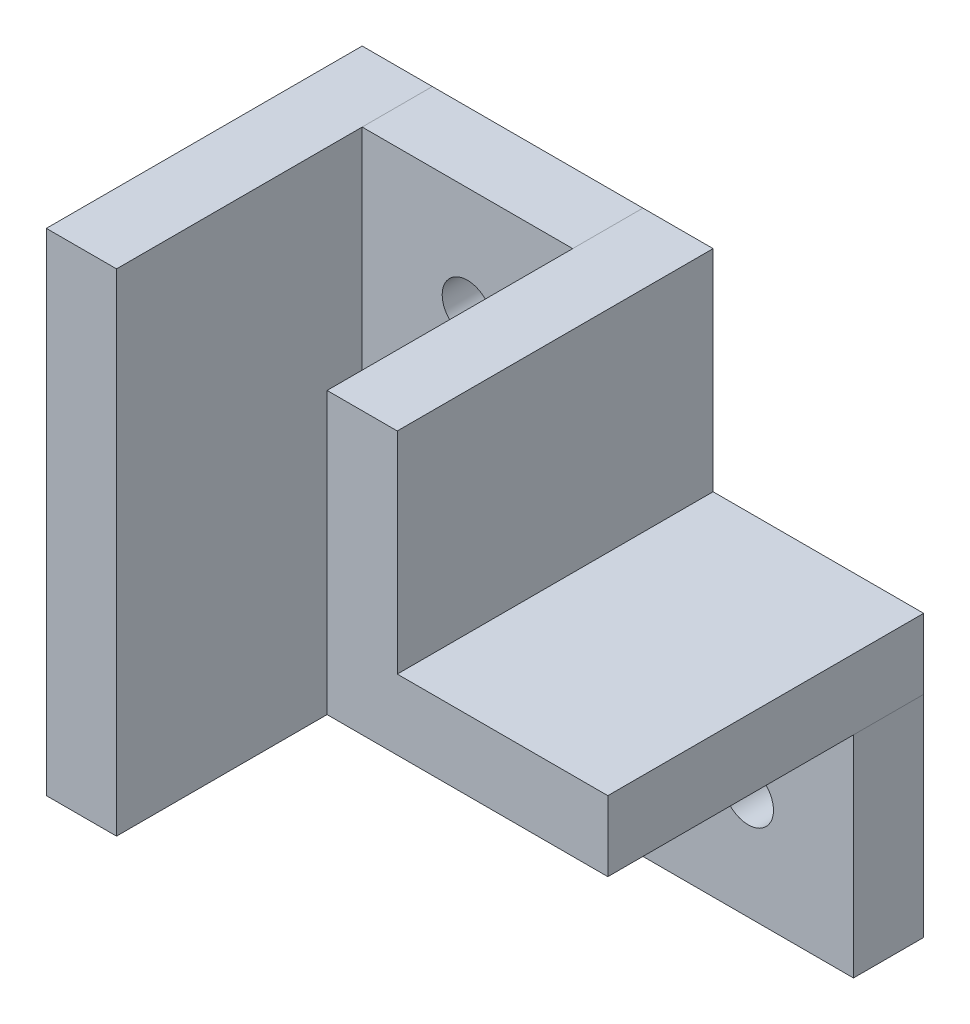
SolidWorks part; units mm, degrees
ref_plane "前视基准面" through (0, 0, 0) normal (0, 0, 1) x (1, 0, 0)
ref_plane "上视基准面" through (0, 0, 0) normal (0, 1, 0) x (1, 0, 0)
ref_plane "右视基准面" through (0, 0, 0) normal (1, 0, 0) x (0, 0, -1)
sketch "Sketch1" plane through (0, 0, 0) normal (0, 0, 1) x (1, 0, 0)
  line L0 (-7.5299, -25.8068) -> (27.4701, -25.8068)
  line L3 (-7.5299, 9.1932) -> (7.4701, 9.1932)
  line L4 (-7.5299, 9.1932) -> (-7.5299, -25.8068)
  line L6 (7.4701, 9.1932) -> (7.4701, -10.8068)
  line L7 (27.4701, -25.8068) -> (27.4701, -10.8068)
  line L8 (27.4701, -10.8068) -> (7.4701, -10.8068)
  dimension "D1" = 15
  dimension "D2" = 35
  dimension "D3" = 35
  dimension "D4" = 15
extrude "Boss-Extrude1" add sketch "Sketch1" along normal blind 5
sketch "Sketch2" plane through (0, 0, 0) normal (0, 0, -1) x (-1, 0, 0)
  line L0 (-7.4701, 9.1932) -> (-12.4701, 9.1932)
  line L1 (-12.4701, 9.1932) -> (-12.4701, -5.8068)
  line L2 (-12.4701, -5.8068) -> (-27.4701, -5.8068)
  line L3 (-27.4701, -10.8068) -> (-27.4701, -5.8068)
  line L4 (-27.4701, -10.8068) -> (-7.4701, -10.8068)
  line L5 (-7.4701, -10.8068) -> (-7.4701, 9.1932)
  dimension "D1" = 5
  dimension "D2" = 5
extrude "Boss-Extrude2" add sketch "Sketch2" against normal blind 22.5 separate body
sketch "Sketch3" plane through (0, 0, 0) normal (0, 0, -1) x (-1, 0, 0)
  line L0 (7.5299, 9.1932) -> (12.5299, 9.1932)
  line L1 (7.5299, -25.8068) -> (12.5299, -25.8068)
  line L2 (12.5299, -25.8068) -> (12.5299, 9.1932)
  line L3 (7.5299, -25.8068) -> (7.5299, 9.1932)
  dimension "D1" = 5
extrude "Boss-Extrude3" add sketch "Sketch3" against normal blind 22.5 separate body
sketch "Sketch4" plane through (0, 0, 0) normal (0, 0, -1) x (-1, 0, 0)
  line L0 (-27.4701, -10.8068) -> (-7.4701, -10.8068) construction
  line L1 (-27.4701, -25.8068) -> (-27.4701, -10.8068) construction
  line L2 (-7.4701, -10.8068) -> (-7.4701, 9.1932) construction
  line L3 (-7.4701, 9.1932) -> (7.5299, 9.1932) construction
  circle A0 centre (0.0299, 1.6932) radius 1.8
  circle A1 centre (-19.9701, -18.3068) radius 1.8
  dimension "D1" = 3.6
  dimension "D2" = 3.6
  dimension "D3" = 7.5
  dimension "D4" = 7.5
  dimension "D5" = 7.5
  dimension "D6" = 7.5
extrude "Cut-Extrude1" cut sketch "Sketch4" against normal through all
